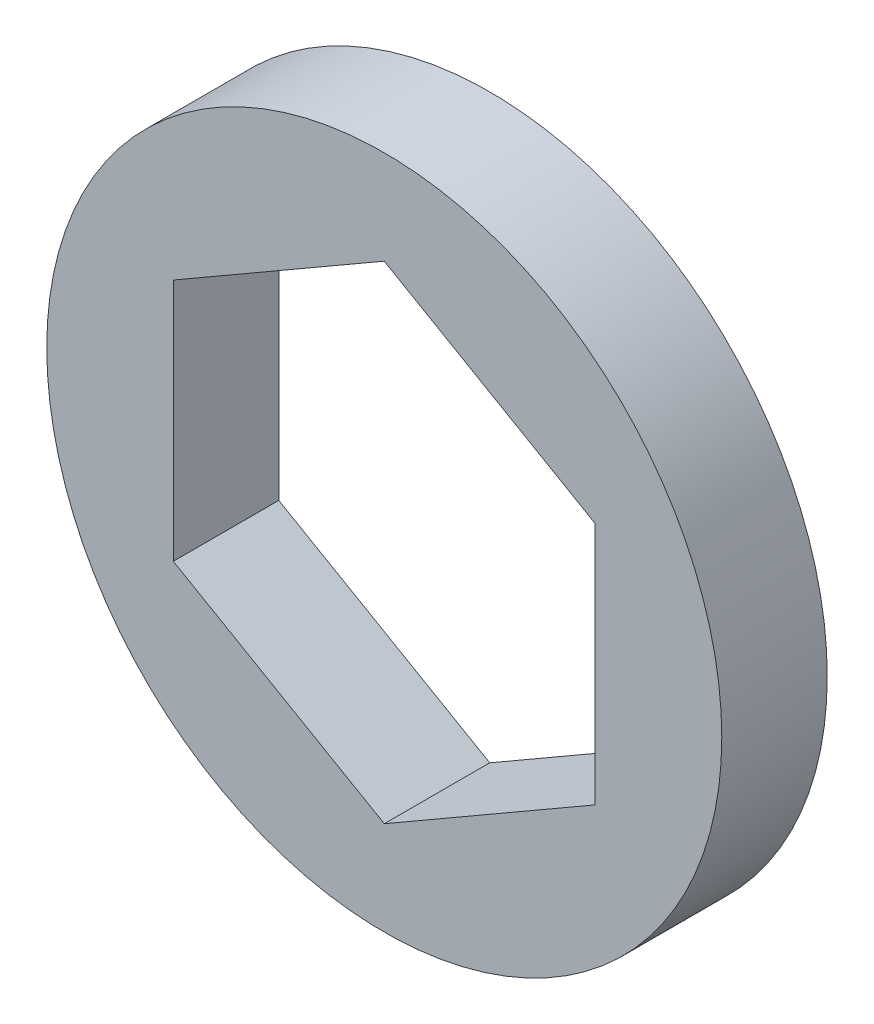
SolidWorks part; units mm, degrees
ref_plane "Front Plane" through (0, 0, 0) normal (0, 0, 1) x (1, 0, 0)
ref_plane "Top Plane" through (0, 0, 0) normal (0, 1, 0) x (1, 0, 0)
ref_plane "Right Plane" through (0, 0, 0) normal (1, 0, 0) x (0, 0, -1)
sketch "Sketch1" plane through (0, 0, 0) normal (0, 0, 1) x (1, 0, 0)
  line L1 (0, 7.3323) -> (-6.35, 3.6662)
  line L2 (-6.35, 3.6662) -> (-6.35, -3.6662)
  line L3 (-6.35, -3.6662) -> (0, -7.3323)
  line L4 (0, -7.3323) -> (6.35, -3.6662)
  line L5 (6.35, -3.6662) -> (6.35, 3.6662)
  line L6 (6.35, 3.6662) -> (0, 7.3323)
  circle A0 centre (0, 0) radius 6.35 construction
  circle A1 centre (0, 0) radius 10.16
  dimension "D1" = 20.32
extrude "Boss-Extrude1" add sketch "Sketch1" along normal blind 3.175
